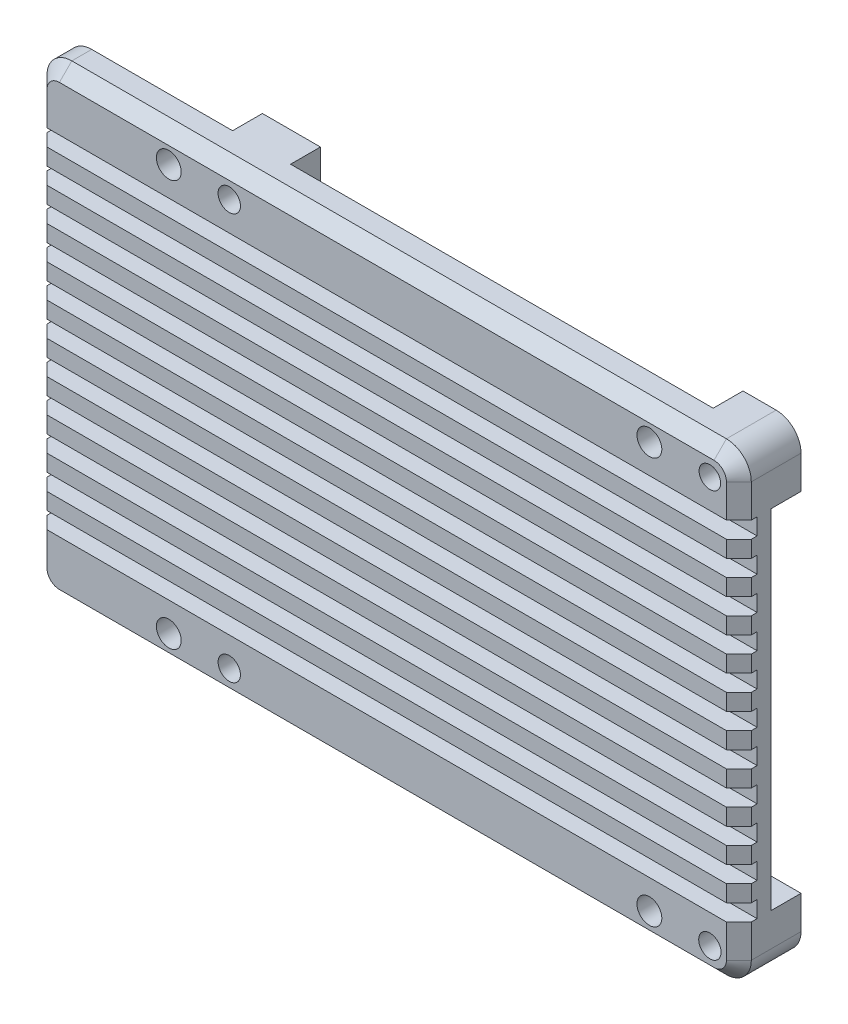
SolidWorks part; units mm, degrees
ref_plane "Front Plane" through (0, 0, 0) normal (0, 0, 1) x (1, 0, 0)
ref_plane "Top Plane" through (0, 0, 0) normal (0, 1, 0) x (1, 0, 0)
ref_plane "Right Plane" through (0, 0, 0) normal (1, 0, 0) x (0, 0, -1)
sketch "Sketch1" plane through (0, 0, 0) normal (0, 0, 1) x (1, 0, 0)
  line L4 (42.5, -25) -> (42.5, 25)
  line L5 (39.5, 28) -> (-39.5, 28)
  line L6 (-42.5, 25) -> (-42.5, -25)
  line L7 (-39.5, -28) -> (39.5, -28)
  line L8 (42.5, -25) -> (42.5, 25)
  line L9 (39.5, 28) -> (-39.5, 28)
  line L10 (-42.5, 25) -> (-42.5, -25)
  line L11 (-39.5, -28) -> (39.5, -28)
  circle A0 centre (-19, -24.5) radius 1.35 construction
  circle A1 centre (39, -24.5) radius 1.35 construction
  circle A2 centre (39, 24.5) radius 1.3 construction
  circle A3 centre (-19, 24.5) radius 1.35 construction
  arc A4 (39.5, -28) -> (42.5, -25) centre (39.5, -25) ccw
  arc A5 (42.5, 25) -> (39.5, 28) centre (39.5, 25) ccw
  arc A6 (-39.5, 28) -> (-42.5, 25) centre (-39.5, 25) ccw
  arc A7 (-42.5, -25) -> (-39.5, -28) centre (-39.5, -25) ccw
  arc A8 (39.5, -28) -> (42.5, -25) centre (39.5, -25) ccw
  arc A9 (42.5, 25) -> (39.5, 28) centre (39.5, 25) ccw
  arc A10 (-39.5, 28) -> (-42.5, 25) centre (-39.5, 25) ccw
  arc A11 (-42.5, -25) -> (-39.5, -28) centre (-39.5, -25) ccw
  circle A12 centre (-19, -24.5) radius 1.35
  circle A13 centre (39, -24.5) radius 1.35
  circle A14 centre (39, 24.5) radius 1.3
  circle A15 centre (-19, 24.5) radius 1.35
  dimension "D1" = 0
extrude "Boss-Extrude1" add sketch "Sketch1" along normal blind 7.5
sketch "Sketch2" plane through (0, 0, 0) normal (0, 0, -1) x (-1, 0, 0)
  line L1 (-35.5, 28) -> (-42.5, 28)
  line L2 (-35.5, 28) -> (-35.5, 21)
  line L3 (-35.5, 21) -> (-42.5, 21)
  line L4 (-39.5, -28) -> (39.5, -28)
  line L5 (42.5, -25) -> (42.5, 25)
  line L6 (39.5, 28) -> (-39.5, 28)
  line L7 (-42.5, 25) -> (-42.5, -25)
  line L8 (-39.5, -28) -> (39.5, -28)
  line L9 (42.5, -25) -> (42.5, 25)
  line L10 (39.5, 28) -> (-39.5, 28)
  line L11 (-42.5, 25) -> (-42.5, -25)
  line L12 (-42.5, 28) -> (-42.5, 21)
  line L13 (-35.5, 28) -> (-42.5, 21) construction
  line L14 (-35.5, 21) -> (-42.5, 28) construction
  line L15 (15.5, 28) -> (22.5, 28)
  line L16 (15.5, 28) -> (15.5, 21)
  line L17 (15.5, 21) -> (22.5, 21)
  line L18 (22.5, 28) -> (22.5, 21)
  line L19 (15.5, 28) -> (22.5, 21) construction
  line L20 (15.5, 21) -> (22.5, 28) construction
  line L21 (22.5, -21) -> (15.5, -21)
  line L22 (22.5, -21) -> (22.5, -28)
  line L23 (22.5, -28) -> (15.5, -28)
  line L24 (15.5, -21) -> (15.5, -28)
  line L25 (22.5, -21) -> (15.5, -28) construction
  line L26 (22.5, -28) -> (15.5, -21) construction
  line L27 (-42.5, -21) -> (-35.5, -21)
  line L28 (-42.5, -21) -> (-42.5, -28)
  line L29 (-42.5, -28) -> (-35.5, -28)
  line L30 (-35.5, -21) -> (-35.5, -28)
  line L31 (-42.5, -21) -> (-35.5, -28) construction
  line L32 (-42.5, -28) -> (-35.5, -21) construction
  arc A4 (-42.5, -25) -> (-39.5, -28) centre (-39.5, -25) ccw
  arc A5 (39.5, -28) -> (42.5, -25) centre (39.5, -25) ccw
  arc A6 (42.5, 25) -> (39.5, 28) centre (39.5, 25) ccw
  arc A7 (-39.5, 28) -> (-42.5, 25) centre (-39.5, 25) ccw
  arc A8 (-42.5, -25) -> (-39.5, -28) centre (-39.5, -25) ccw
  arc A9 (39.5, -28) -> (42.5, -25) centre (39.5, -25) ccw
  arc A10 (42.5, 25) -> (39.5, 28) centre (39.5, 25) ccw
  arc A11 (-39.5, 28) -> (-42.5, 25) centre (-39.5, 25) ccw
  point P0 (-39, 24.5)
  point P16 (19, 24.5)
  point P24 (19, -24.5)
  point P30 (-39, -24.5)
  arc M21 (39.5, -28) -> (42.5, -25) centre (39.5, -25) ccw
  line M22 (42.5, -25) -> (42.5, 25)
  arc M23 (42.5, 25) -> (39.5, 28) centre (39.5, 25) ccw
  line M24 (39.5, 28) -> (-39.5, 28)
  line M26 (-42.5, 25) -> (-42.5, -25)
  dimension "D1" = 0
extrude "Cut-Extrude1" cut sketch "Sketch2" against normal blind 3.6 contours L27 L30 L8 L24 L21 L22 L18 L17 L16 L2 L3 M21 M22 M23 M24 M26
chamfer "Chamfer1" distance 1.5 angle 45 8 edges at (0, -28, 7.5) (41.6213, -27.1213, 7.5) (-41.6213, -27.1213, 7.5) (42.5, 0, 7.5) (-42.5, 0, 7.5) (41.6213, 27.1213, 7.5) (-41.6213, 27.1213, 7.5) (0, 28, 7.5)
sketch "Sketch3" plane through (0, 0, 7.5) normal (0, 0, 1) x (1, 0, 0)
  line L1 (-42.5, 21) -> (42.5, 21)
  line L2 (-42.5, 21) -> (-42.5, 19)
  line L3 (-42.5, 19) -> (42.5, 19)
  line L4 (42.5, 21) -> (42.5, 19)
  line L6 (-39.5, 28) -> (39.5, 28) construction
  line L7 (-42.5, 15) -> (42.5, 15)
  line L8 (42.5, 17) -> (42.5, 15)
  line L9 (-42.5, 17) -> (42.5, 17)
  line L10 (-42.5, 17) -> (-42.5, 15)
  line L11 (-42.5, 11) -> (42.5, 11)
  line L12 (42.5, 13) -> (42.5, 11)
  line L13 (-42.5, 13) -> (42.5, 13)
  line L14 (-42.5, 13) -> (-42.5, 11)
  line L15 (-42.5, 7) -> (42.5, 7)
  line L16 (42.5, 9) -> (42.5, 7)
  line L17 (-42.5, 9) -> (42.5, 9)
  line L18 (-42.5, 9) -> (-42.5, 7)
  line L19 (-42.5, 3) -> (42.5, 3)
  line L20 (42.5, 5) -> (42.5, 3)
  line L21 (-42.5, 5) -> (42.5, 5)
  line L22 (-42.5, 5) -> (-42.5, 3)
  line L23 (-42.5, -1) -> (42.5, -1)
  line L24 (42.5, 1) -> (42.5, -1)
  line L25 (-42.5, 1) -> (42.5, 1)
  line L26 (-42.5, 1) -> (-42.5, -1)
  line L27 (-42.5, -5) -> (42.5, -5)
  line L28 (42.5, -3) -> (42.5, -5)
  line L29 (-42.5, -3) -> (42.5, -3)
  line L30 (-42.5, -3) -> (-42.5, -5)
  line L31 (-42.5, -9) -> (42.5, -9)
  line L32 (42.5, -7) -> (42.5, -9)
  line L33 (-42.5, -7) -> (42.5, -7)
  line L34 (-42.5, -7) -> (-42.5, -9)
  line L35 (-42.5, -13) -> (42.5, -13)
  line L36 (42.5, -11) -> (42.5, -13)
  line L37 (-42.5, -11) -> (42.5, -11)
  line L38 (-42.5, -11) -> (-42.5, -13)
  line L39 (-42.5, -17) -> (42.5, -17)
  line L40 (42.5, -15) -> (42.5, -17)
  line L41 (-42.5, -15) -> (42.5, -15)
  line L42 (-42.5, -15) -> (-42.5, -17)
  line L43 (-42.5, -21) -> (42.5, -21)
  line L44 (42.5, -19) -> (42.5, -21)
  line L45 (-42.5, -19) -> (42.5, -19)
  line L46 (-42.5, -19) -> (-42.5, -21)
  line L47 (-42.5, -25) -> (-42.5, 25) construction
  line L48 (42.5, 25) -> (42.5, -25) construction
  point P4 (-42.5, 21)
  point P6 (42.5, 19)
  point P10 (0, 0)
  point P52 (0, 0)
  dimension "D1" = 2
  dimension "D2" = 7
  dimension "D4" = 4
  dimension "D3" = 11
extrude "Cut-Extrude2" cut sketch "Sketch3" against normal blind 2.2
sketch "Sketch4" plane through (0, 0, 7.5) normal (0, 0, 1) x (1, 0, 0)
  line L0 (-19, 24.5) -> (39, 24.5) construction
  line L1 (-42.5, 0) -> (42.5, 0) construction
  line L2 (-42.5, 1) -> (-42.5, -1) construction
  line L3 (42.5, -1) -> (42.5, 1) construction
  line L4 (31.7, 24.5) -> (39, 24.5) construction
  line L5 (-26.3, 24.5) -> (-19, 24.5) construction
  circle A0 centre (-26.3, 24.5) radius 1.5
  circle A1 centre (31.7, 24.5) radius 1.5
  circle A2 centre (-26.3, -24.5) radius 1.5
  circle A3 centre (31.7, -24.5) radius 1.5
  dimension "D1" = 3
  dimension "D2" = 7.3
extrude "Cut-Extrude3" cut sketch "Sketch4" against normal up to next
